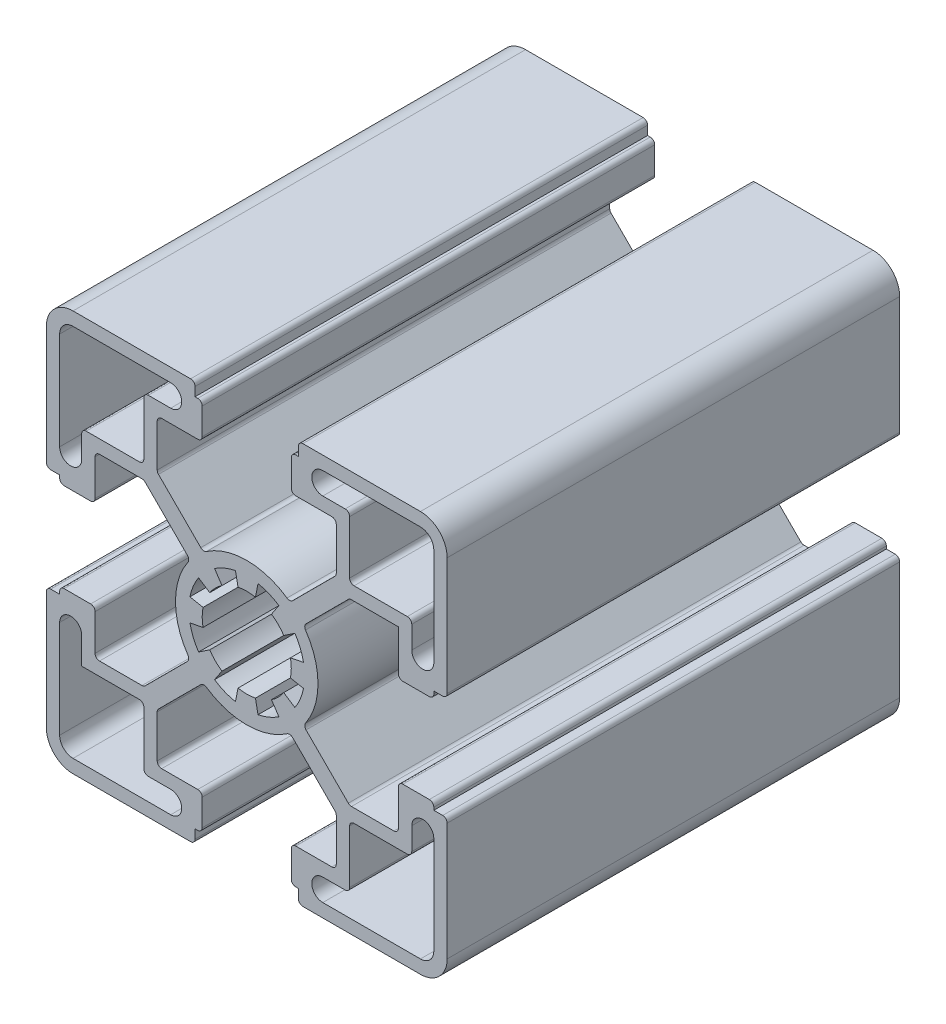
SolidWorks part; units mm, degrees
ref_plane "Front Plane" through (0, 0, 0) normal (0, 0, 1) x (1, 0, 0)
ref_plane "Top Plane" through (0, 0, 0) normal (0, 1, 0) x (1, 0, 0)
ref_plane "Right Plane" through (0, 0, 0) normal (1, 0, 0) x (0, 0, -1)
sketch "Sketch1" plane through (0, 0, 0) normal (0, 0, 1) x (1, 0, 0)
  line L0 (0, 22.5) -> (0, -22.5) construction
  line L1 (22.5, 0) -> (-22.5, 0) construction
  line L2 (-5.8, 22.5) -> (5.8, 22.5) construction
  line L3 (-5, 21) -> (5, 21) construction
  line L4 (-10.05, 10.05) -> (10.05, 10.05) construction
  line L5 (0, 0) -> (-10.05, 10.05) construction
  circle A0 centre (0, 0) radius 5 construction
  point P4 (0, 0)
  point P8 (0, 0)
  point P10 (0, 8)
  point P14 (0, 22.5)
  point P17 (0, 21)
  point P19 (0, 10.05)
sketch "Sketch2" plane through (0, 0, 0) normal (1, 0, 0) x (0, 0, -1)
  line L0 (152.4, 0) -> (-152.4, 0) construction
  point P4 (0, 0)
  dimension "D1" = 304.8
sketch "Sketch3" plane through (0, 0, 0) normal (0, 0, 1) x (1, 0, 0)
  line L5 (-21, 8.5375) -> (-21, 19.5)
  line L9 (0, 0) -> (-22.5, 22.5) construction
  line L10 (-11.55, -10.05) -> (-6.3569, -4.8569)
  line L11 (-19.5, 21) -> (-8.5375, 21)
  line L38 (-5.8, 22.5) -> (-5.8, 21)
  line L46 (-5.8, 21) -> (-5, 21)
  line L62 (-5, 21) -> (-5, 17.025)
  line L74 (-5, 17.025) -> (-10.05, 17.025)
  line L76 (-10.05, 17.025) -> (-10.05, 11.55)
  line L77 (-10.05, 11.55) -> (-4.8569, 6.3569)
  line L78 (-18.525, 8.5375) -> (-18.525, 11.55)
  line L79 (-10.05, 17.025) -> (-10.05, 22.5) construction
  line L80 (0, 22.5) -> (0, -22.5) construction
  line L81 (-5.8, 22.5) -> (5.8, 22.5) construction
  line L82 (10.05, 11.55) -> (4.8569, 6.3569)
  line L83 (10.05, 17.025) -> (10.05, 11.55)
  line L84 (5, 17.025) -> (10.05, 17.025)
  line L85 (5, 21) -> (5, 17.025)
  line L86 (5.8, 21) -> (5, 21)
  line L87 (5.8, 22.5) -> (5.8, 21)
  line L88 (-22.5, -5.8) -> (-21, -5.8)
  line L89 (-21, -5.8) -> (-21, -5)
  line L90 (-21, -5) -> (-17.025, -5)
  line L91 (-17.025, -5) -> (-17.025, -10.05)
  line L92 (-17.025, -10.05) -> (-11.55, -10.05)
  line L93 (-11.55, -10.05) -> (-6.3569, -4.8569)
  line L94 (-11.55, 10.05) -> (-6.3569, 4.8569)
  line L95 (-17.025, 10.05) -> (-11.55, 10.05)
  line L96 (-17.025, 5) -> (-17.025, 10.05)
  line L97 (-21, 5) -> (-17.025, 5)
  line L98 (-21, 5.8) -> (-21, 5)
  line L99 (-22.5, 5.8) -> (-21, 5.8)
  line L100 (-22.5, 5.8) -> (-22.5, 19.5)
  line L101 (-19.5, 22.5) -> (-5.8, 22.5)
  line L102 (-18.525, 11.55) -> (-11.55, 11.55)
  line L103 (-8.5375, 18.525) -> (-11.55, 18.525)
  line L104 (-11.55, 18.525) -> (-11.55, 11.55)
  line L108 (5.8, -22.5) -> (5.8, -21)
  line L113 (5.8, -21) -> (5, -21)
  line L117 (5.8, 22.5) -> (19.5, 22.5)
  line L118 (22.5, 19.5) -> (22.5, 5.8)
  line L119 (19.5, -22.5) -> (5.8, -22.5)
  line L120 (0, 0) -> (22.5, 0) construction
  line L121 (-22.5, -19.5) -> (-22.5, -5.8)
  line L136 (5, -21) -> (5, -17.025)
  line L137 (5, -17.025) -> (10.05, -17.025)
  line L138 (10.05, -17.025) -> (10.05, -11.55)
  line L139 (10.05, -11.55) -> (4.8569, -6.3569)
  line L140 (-10.05, -11.55) -> (-4.8569, -6.3569)
  line L141 (-10.05, -17.025) -> (-10.05, -11.55)
  line L142 (-5, -17.025) -> (-10.05, -17.025)
  line L143 (-5, -21) -> (-5, -17.025)
  line L144 (-5.8, -21) -> (-5, -21)
  line L145 (-5.8, -22.5) -> (-5.8, -21)
  line L146 (-5.8, -22.5) -> (-19.5, -22.5)
  line L147 (22.5, 5.8) -> (21, 5.8)
  line L148 (21, 5.8) -> (21, 5)
  line L149 (21, 5) -> (17.025, 5)
  line L150 (17.025, 5) -> (17.025, 10.05)
  line L151 (17.025, 10.05) -> (11.55, 10.05)
  line L152 (11.55, 10.05) -> (6.3569, 4.8569)
  line L153 (11.55, -10.05) -> (6.3569, -4.8569)
  line L154 (17.025, -10.05) -> (11.55, -10.05)
  line L155 (17.025, -5) -> (17.025, -10.05)
  line L156 (21, -5) -> (17.025, -5)
  line L157 (21, -5.8) -> (21, -5)
  line L158 (22.5, -5.8) -> (21, -5.8)
  line L159 (11.55, -10.05) -> (6.3569, -4.8569)
  line L160 (22.5, -5.8) -> (22.5, -19.5)
  line L161 (8.5375, 21) -> (19.5, 21)
  line L162 (21, 19.5) -> (21, 8.5375)
  line L163 (8.5375, 18.525) -> (11.55, 18.525)
  line L164 (11.55, 18.525) -> (11.55, 11.55)
  line L165 (18.525, 8.5375) -> (18.525, 11.55)
  line L166 (18.525, 11.55) -> (11.55, 11.55)
  line L167 (21, -8.5375) -> (21, -19.5)
  line L168 (19.5, -21) -> (8.5375, -21)
  line L169 (18.525, -8.5375) -> (18.525, -11.55)
  line L170 (18.525, -11.55) -> (11.55, -11.55)
  line L171 (8.5375, -18.525) -> (11.55, -18.525)
  line L172 (11.55, -18.525) -> (11.55, -11.55)
  line L173 (-8.5375, -21) -> (-19.5, -21)
  line L174 (-21, -19.5) -> (-21, -8.5375)
  line L175 (-8.5375, -18.525) -> (-11.55, -18.525)
  line L176 (-11.55, -18.525) -> (-11.55, -11.55)
  line L177 (-18.525, -8.5375) -> (-18.525, -11.55)
  line L178 (-18.525, -11.55) -> (-11.55, -11.55)
  line L179 (0, 0) -> (-11.55, 11.55) construction
  line L180 (0, 0) -> (11.55, 11.55) construction
  arc A2 (-21, 19.5) -> (-19.5, 21) centre (-19.5, 19.5) cw
  arc A73 (-4.8569, 6.3569) -> (4.8569, 6.3569) centre (0, 0) cw
  arc A74 (-6.3569, 4.8569) -> (-6.3569, -4.8569) centre (0, 0) ccw
  arc A75 (-19.5, 22.5) -> (-22.5, 19.5) centre (-19.5, 19.5) ccw
  arc A76 (-21, 8.5375) -> (-18.525, 8.5375) centre (-19.7625, 8.5375) ccw
  arc A77 (-8.5375, 21) -> (-8.5375, 18.525) centre (-8.5375, 19.7625) cw
  arc A80 (19.5, 22.5) -> (22.5, 19.5) centre (19.5, 19.5) cw
  arc A81 (22.5, -19.5) -> (19.5, -22.5) centre (19.5, -19.5) cw
  arc A82 (-19.5, -22.5) -> (-22.5, -19.5) centre (-19.5, -19.5) cw
  circle A88 centre (0, 0) radius 5 construction
  circle A89 centre (0, 0) radius 5
  arc A90 (-4.8569, -6.3569) -> (4.8569, -6.3569) centre (0, 0) ccw
  arc A91 (19.5, 21) -> (21, 19.5) centre (19.5, 19.5) cw
  arc A92 (6.3569, 4.8569) -> (6.3569, -4.8569) centre (0, 0) cw
  arc A93 (8.5375, 21) -> (8.5375, 18.525) centre (8.5375, 19.7625) ccw
  arc A94 (21, 8.5375) -> (18.525, 8.5375) centre (19.7625, 8.5375) cw
  arc A95 (21, -19.5) -> (19.5, -21) centre (19.5, -19.5) cw
  arc A96 (21, -8.5375) -> (18.525, -8.5375) centre (19.7625, -8.5375) ccw
  arc A97 (8.5375, -21) -> (8.5375, -18.525) centre (8.5375, -19.7625) cw
  arc A98 (-19.5, -21) -> (-21, -19.5) centre (-19.5, -19.5) cw
  arc A99 (-8.5375, -21) -> (-8.5375, -18.525) centre (-8.5375, -19.7625) ccw
  arc A100 (-21, -8.5375) -> (-18.525, -8.5375) centre (-19.7625, -8.5375) cw
  point P54 (-14.2875, 10.05)
  dimension "D2" = 3
  dimension "D3" = 1.5
  dimension "D4" = 1.5
  dimension "D5" = 1.5
  dimension "D6" = 90
  dimension "D1" = 4
extrude "Boss-Extrude1" add sketch "Sketch3" along normal blind 50.8 contours A92 L152 L151 L150 L149 L148 L147 L118 A80 L117 L87 L86 L85 L84 L83 L82 A73 L77 L76 L74 L62 L46 L38 L101 A75 L100 L99 L98 L97 L96 L95 L94 A74 L10 L92 L91 L90 L89 L88 L121 A82 L146 L145 L144 L143 L142 L141 L140 A90 L139 L138
fillet "Fillet1" radius 0.5 58 edges at (5, 21, 25.4) (5.8, 22.5, 25.4) (-5.8, 22.5, 25.4) (-5, 21, 25.4) (-10.05, 17.025, 25.4) (-5, 17.025, 25.4) (5, 17.025, 25.4) (-22.5, -5.8, 25.4) (-21, -5, 25.4) (-17.025, -5, 25.4) (-17.025, -10.05, 25.4) (-11.55, -10.05, 25.4) (-6.3569, -4.8569, 25.4) (-6.3569, 4.8569, 25.4) (-11.55, 10.05, 25.4) (-17.025, 10.05, 25.4) (-17.025, 5, 25.4) (-22.5, 5.8, 25.4) (-21, 5, 25.4) (-18.525, 11.55, 25.4) (-11.55, 11.55, 25.4) (-11.55, 18.525, 25.4) (4.8569, 6.3569, 25.4) (-4.8569, 6.3569, 25.4) (-10.05, 11.55, 25.4) (10.05, 17.025, 25.4) (10.05, 11.55, 25.4) (22.5, -5.8, 25.4) (21, -5, 25.4) (17.025, -5, 25.4) (17.025, -10.05, 25.4) (6.3569, 4.8569, 25.4) (11.55, 10.05, 25.4) (22.5, 5.8, 25.4) (21, 5, 25.4) (17.025, 5, 25.4) (4.8569, -6.3569, 25.4) (11.55, -11.55, 25.4) (-11.55, -11.55, 25.4) (18.525, -11.55, 25.4) (11.55, -18.525, 25.4) (10.05, -17.025, 25.4) (5, -17.025, 25.4) (5, -21, 25.4) (5.8, -22.5, 25.4) (-5.8, -22.5, 25.4) (-5, -21, 25.4) (-5, -17.025, 25.4) (-10.05, -17.025, 25.4) (-11.55, -18.525, 25.4) (11.55, 18.525, 25.4) (18.525, 11.55, 25.4) (11.55, 11.55, 25.4) (11.55, -10.05, 25.4) (6.3569, -4.8569, 25.4) (-4.8569, -6.3569, 25.4) (10.05, -11.55, 25.4) (-10.05, -11.55, 25.4)
sketch "Sketch4" plane through (0, 0, 50.8) normal (0, 0, 1) x (1, 0, 0)
  line L0 (-1.2681, 6.3751) -> (-0.9755, 4.9039)
  line L1 (0, 0) -> (0, 8) construction
  line L2 (-3.6112, 5.4046) -> (-2.7779, 4.1573)
  line L3 (1.2681, 6.3751) -> (0.9755, 4.9039)
  line L4 (3.6112, 5.4046) -> (2.7779, 4.1573)
  line L5 (5.4046, 3.6112) -> (4.1573, 2.7779)
  line L6 (6.3751, 1.2681) -> (4.9039, 0.9755)
  line L7 (6.3751, -1.2681) -> (4.9039, -0.9755)
  line L8 (5.4046, -3.6112) -> (4.1573, -2.7779)
  line L9 (3.6112, -5.4046) -> (2.7779, -4.1573)
  line L10 (1.2681, -6.3751) -> (0.9755, -4.9039)
  line L11 (-1.2681, -6.3751) -> (-0.9755, -4.9039)
  line L12 (-3.6112, -5.4046) -> (-2.7779, -4.1573)
  line L13 (-5.4046, -3.6112) -> (-4.1573, -2.7779)
  line L14 (-6.3751, -1.2681) -> (-4.9039, -0.9755)
  line L15 (-6.3751, 1.2681) -> (-4.9039, 0.9755)
  line L16 (-5.4046, 3.6112) -> (-4.1573, 2.7779)
  line L17 (0, 0) -> (-0.9755, 4.9039) construction
  line L18 (0, 0) -> (2.7779, 4.1573) construction
  arc A0 (-1.2681, 6.3751) -> (-3.6112, 5.4046) centre (0, 0) ccw
  circle A1 centre (0, 0) radius 5 construction
  arc A2 (-0.9755, 4.9039) -> (-2.7779, 4.1573) centre (0, 0) ccw
  arc A4 (2.7779, 4.1573) -> (0.9755, 4.9039) centre (0, 0) ccw
  arc A5 (3.6112, 5.4046) -> (1.2681, 6.3751) centre (0, 0) ccw
  arc A6 (4.9039, 0.9755) -> (4.1573, 2.7779) centre (0, 0) ccw
  arc A7 (6.3751, 1.2681) -> (5.4046, 3.6112) centre (0, 0) ccw
  arc A8 (4.1573, -2.7779) -> (4.9039, -0.9755) centre (0, 0) ccw
  arc A9 (5.4046, -3.6112) -> (6.3751, -1.2681) centre (0, 0) ccw
  arc A10 (0.9755, -4.9039) -> (2.7779, -4.1573) centre (0, 0) ccw
  arc A11 (1.2681, -6.3751) -> (3.6112, -5.4046) centre (0, 0) ccw
  arc A12 (-2.7779, -4.1573) -> (-0.9755, -4.9039) centre (0, 0) ccw
  arc A13 (-3.6112, -5.4046) -> (-1.2681, -6.3751) centre (0, 0) ccw
  arc A14 (-4.9039, -0.9755) -> (-4.1573, -2.7779) centre (0, 0) ccw
  arc A15 (-6.3751, -1.2681) -> (-5.4046, -3.6112) centre (0, 0) ccw
  arc A16 (-4.1573, 2.7779) -> (-4.9039, 0.9755) centre (0, 0) ccw
  arc A17 (-5.4046, 3.6112) -> (-6.3751, 1.2681) centre (0, 0) ccw
  dimension "D1" = 1.5
  dimension "D2" = 22.5
  dimension "D5" = 45
  dimension "D4" = 8
extrude "Cut-Extrude1" cut sketch "Sketch4" against normal through all
equation "\"D3@Sketch3\"=\"Wall@Sketch1\""
equation "\"D4@Sketch3\"=\"Wall@Sketch1\""
equation "\"D5@Sketch3\"=\"Wall@Sketch1\""
equation "\"D1@Sketch4\"=\"Wall@Sketch1\""
